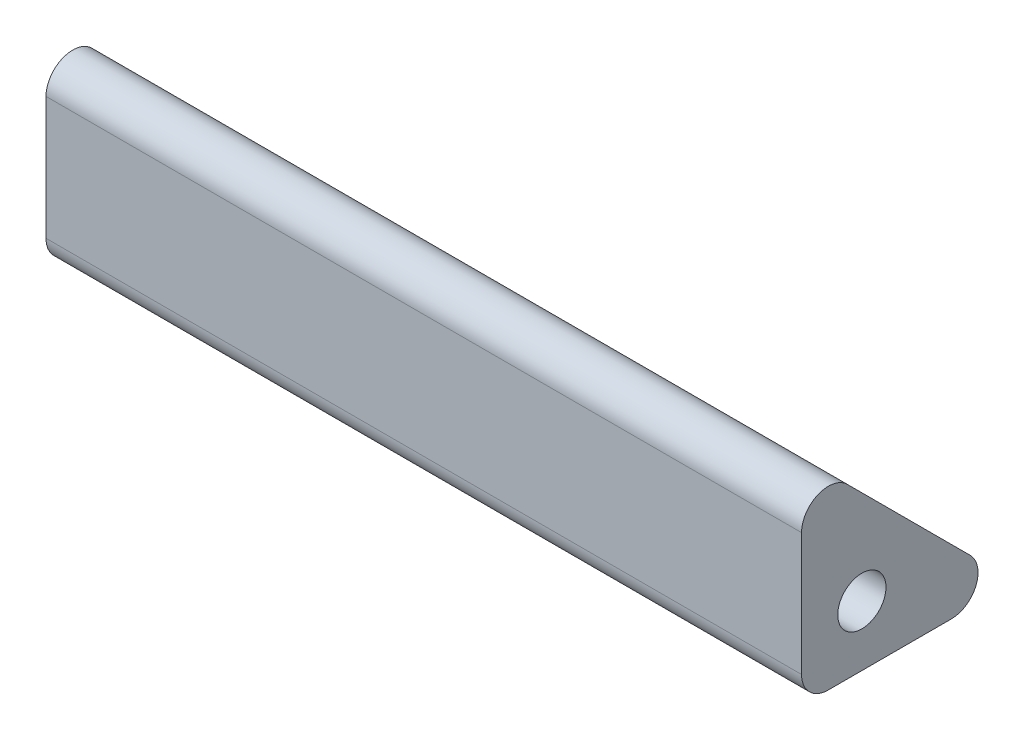
SolidWorks part; units mm, degrees
ref_plane "Front Plane" through (0, 0, 0) normal (0, 0, 1) x (1, 0, 0)
ref_plane "Top Plane" through (0, 0, 0) normal (0, 1, 0) x (1, 0, 0)
ref_plane "Right Plane" through (0, 0, 0) normal (1, 0, 0) x (0, 0, -1)
sketch "Sketch1" plane through (0, 0, 0) normal (1, 0, 0) x (0, 0, -1)
  line L0 (-2.25, 5.75) -> (-2.25, -2.25)
  line L1 (-2.25, -2.25) -> (5.75, -2.25)
  line L3 (-2.25, 5.75) -> (5.75, -2.25)
  circle A0 centre (0, 0) radius 0.9
  dimension "D1" = 1.8
  dimension "D2" = 8
  dimension "D3" = 8
  dimension "D4" = 2.25
  dimension "D5" = 2.25
extrude "Boss-Extrude1" add sketch "Sketch1" along normal blind 28.2
fillet "Fillet1" radius 1 3 edges at (14.1, -2.25, 2.25) (14.1, -2.25, -5.75) (14.1, 5.75, 2.25)
